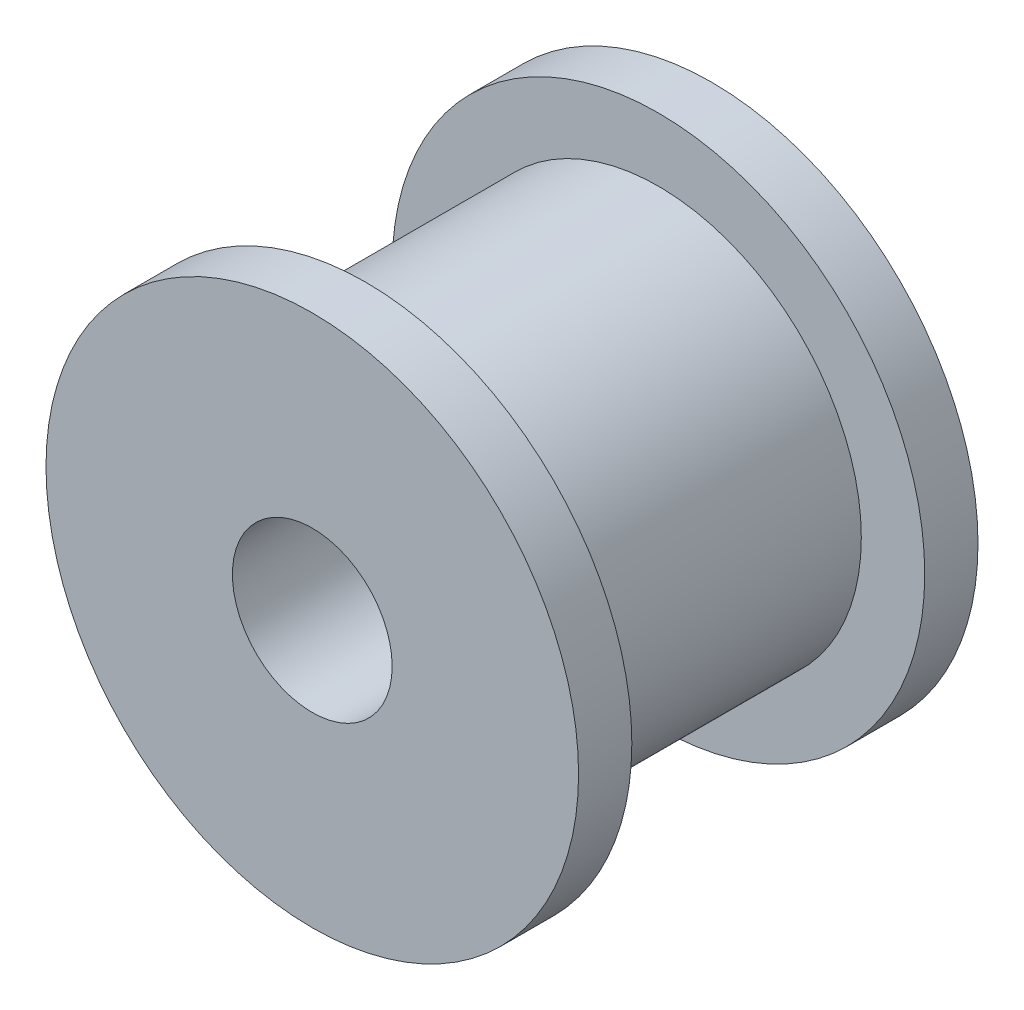
SolidWorks part; units mm, degrees
ref_plane "Front Plane" through (0, 0, 0) normal (0, 0, 1) x (1, 0, 0)
ref_plane "Top Plane" through (0, 0, 0) normal (0, 1, 0) x (1, 0, 0)
ref_plane "Right Plane" through (0, 0, 0) normal (1, 0, 0) x (0, 0, -1)
sketch "Sketch1" plane through (0, 0, 0) normal (0, 0, 1) x (1, 0, 0)
  circle A0 centre (0, 0) radius 10
  circle A1 centre (0, 0) radius 3
  dimension "D1" = 20
  dimension "D2" = 6
extrude "Boss-Extrude1" add sketch "Sketch1" along normal blind 15
sketch "Sketch2" plane through (0, 0, 15) normal (0, 0, 1) x (1, 0, 0)
  circle A0 centre (0, 0) radius 7.6184
  circle A1 centre (0, 0) radius 10.0033
extrude "Cut-Extrude1" cut sketch "Sketch2" against normal offset from surface (11 mm away) 2 from offset 2 up to face at (10, 0, 0)
